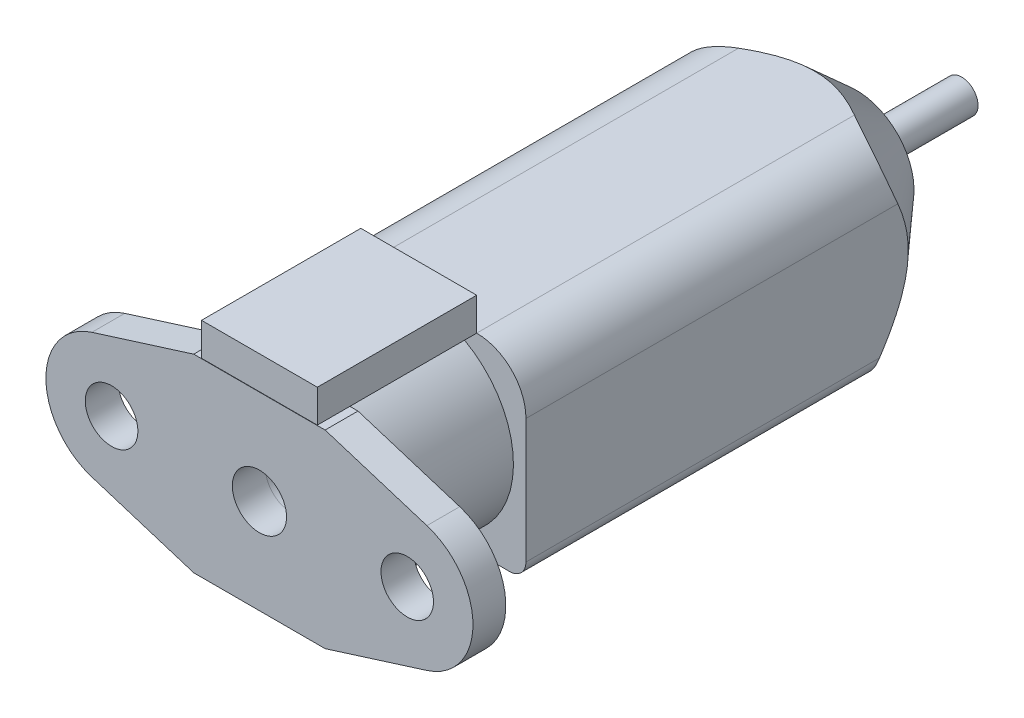
SolidWorks part; units mm, degrees
ref_plane "Alzado" through (0, 0, 0) normal (0, 0, 1) x (1, 0, 0)
ref_plane "Planta" through (0, 0, 0) normal (0, 1, 0) x (1, 0, 0)
ref_plane "Vista lateral" through (0, 0, 0) normal (1, 0, 0) x (0, 0, -1)
sketch "Croquis1" plane through (0, 0, 0) normal (0, 0, 1) x (1, 0, 0)
  line L0 (4, 5.763) -> (10.196, 3.8191)
  line L1 (-4, 5.763) -> (-10.1991, 3.8155)
  line L2 (-4, -5.765) -> (-10.1991, -3.8177)
  line L3 (4, -5.765) -> (10.1978, -3.8173)
  line L4 (4, -5.765) -> (-4, -5.765)
  line L5 (-4, 5.763) -> (4, 5.763)
  circle A0 centre (8.998, 0.0006) radius 1.5982
  circle A1 centre (-9.0001, -0.0011) radius 1.601
  circle A2 centre (0, 0) radius 1.6509
  arc A3 (10.1978, -3.8173) -> (10.196, 3.8191) centre (8.998, 0.0006) ccw
  arc A4 (-10.1991, 3.8155) -> (-10.1991, -3.8177) centre (-9.0001, -0.0011) ccw
extrude "Saliente-Extruir7" add sketch "Croquis1" against normal blind 2 separate body
sketch "Croquis2" plane through (0, 0, -2) normal (0, 0, -1) x (-1, 0, 0)
  circle A0 centre (0, 0) radius 5.765
  circle A1 centre (0, 0) radius 1.6512
extrude "Saliente-Extruir8" add sketch "Croquis2" along normal blind 7.7
sketch "Croquis3" plane through (0, 0, -9.7) normal (0, 0, -1) x (-1, 0, 0)
  line L1 (3.5269, 5.7838) -> (-3.5269, 5.7838)
  line L2 (6.5269, 2.7838) -> (6.5269, -4.7838)
  line L3 (5.5269, -5.7838) -> (-5.5269, -5.7838)
  line L4 (-6.5269, 2.7838) -> (-6.5269, -4.7838)
  line L5 (6.5269, 5.7838) -> (-6.5269, -5.7838) construction
  line L6 (6.5269, -5.7838) -> (-6.5269, 5.7838) construction
  arc A0 (-3.5269, 5.7838) -> (-6.5269, 2.7838) centre (-3.5269, 2.7838) ccw
  arc A1 (3.5269, 5.7838) -> (6.5269, 2.7838) centre (3.5269, 2.7838) cw
  arc A2 (-5.5269, -5.7838) -> (-6.5269, -4.7838) centre (-5.5269, -4.7838) cw
  arc A3 (6.5269, -4.7838) -> (5.5269, -5.7838) centre (5.5269, -4.7838) cw
  point P0 (0, 0)
  dimension "D1" = 3
  dimension "D2" = 1
extrude "Saliente-Extruir9" add sketch "Croquis3" along normal blind 26.65
ref_plane "Plano1" through (0, 5.765, 0) normal (0, 1, 0) x (1, 0, 0)
ref_axis "Eje1" through (0, 0, -39.9199) along (0, 0, 1)
sketch "Croquis5" plane through (0, 0, 0) normal (0, 1, 0) x (1, 0, 0)
  line L0 (0, 36.35) -> (-3.5, 36.35) construction
  line L1 (-3.5269, 36.35) -> (3.5269, 36.35) construction
  line L2 (-3.5, 36.35) -> (-8.4726, 30.8035)
  line L3 (-3.5, 36.35) -> (-8.4726, 36.35)
  line L4 (-8.4726, 30.8035) -> (-8.4726, 36.35)
revolve "Cortar-Revolución1" cut sketch "Croquis5" angle 360 about axis through (0, 0, -39.9199) along (0, 0, 1)
sketch "Croquis6" plane through (0, 0, -36.35) normal (0, 0, -1) x (-1, 0, 0)
  circle A0 centre (0, 0) radius 0.9994
extrude "Saliente-Extruir10" add sketch "Croquis6" along normal blind 6.4
sketch "Croquis7" plane through (0, 5.7838, 0) normal (0, 1, 0) x (1, 0, 0)
  line L1 (4, 0) -> (-4, 0) construction
  line L2 (3.5269, 9.7) -> (-3.5269, 9.7)
  line L3 (3.5269, 9.7) -> (3.5269, 0)
  line L4 (3.5269, 0) -> (-3.5269, 0)
  line L5 (-3.5269, 9.7) -> (-3.5269, 0)
  line L6 (3.5269, 9.7) -> (-3.5269, 0) construction
  line L7 (3.5269, 0) -> (-3.5269, 9.7) construction
  point P6 (0, 4.85)
extrude "Saliente-Extruir11" add sketch "Croquis7" along normal blind 2 separate body
sketch "Croquis8" plane through (0, 0, -42.75) normal (0, 0, -1) x (-1, 0, 0)
  circle A1 centre (0, 0) radius 0.9994
  circle A2 centre (0, 0) radius 0.9994
  dimension "D1" = 0
